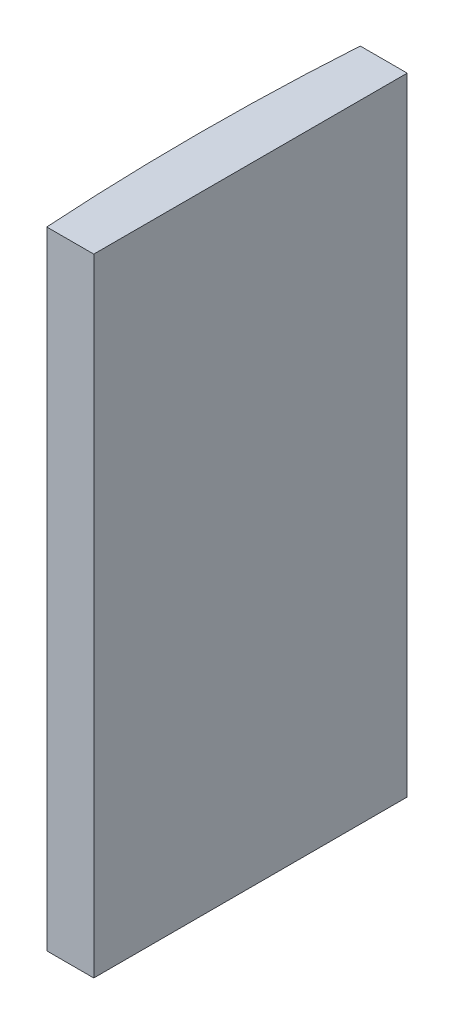
SolidWorks part; units mm, degrees
ref_plane "前视基准面" through (0, 0, 0) normal (0, 0, 1) x (1, 0, 0)
ref_plane "上视基准面" through (0, 0, 0) normal (0, 1, 0) x (1, 0, 0)
ref_plane "右视基准面" through (0, 0, 0) normal (1, 0, 0) x (0, 0, -1)
sketch "草图1" plane through (0, 0, 0) normal (0, 1, 0) x (1, 0, 0)
  line L0 (10.7432, 0) -> (-607.0701, 0) construction
  line L1 (-150.4221, 10) -> (-147.4248, 10)
  line L2 (-150.4221, -10) -> (-147.4248, -10)
  line L3 (-147.4248, 10) -> (-147.4248, -10)
  arc A0 (-150.4221, 10) -> (-150.4221, -10) centre (4.3552, 0) ccw
  point P19 (-150.7448, 0)
  point P20 (-147.4248, 0)
  dimension "D2" = 10
  dimension "D3" = 155.1
  dimension "D4" = 3.32
  dimension "D1" = 10
extrude "凸台-拉伸1" add sketch "草图1" along normal blind 40
